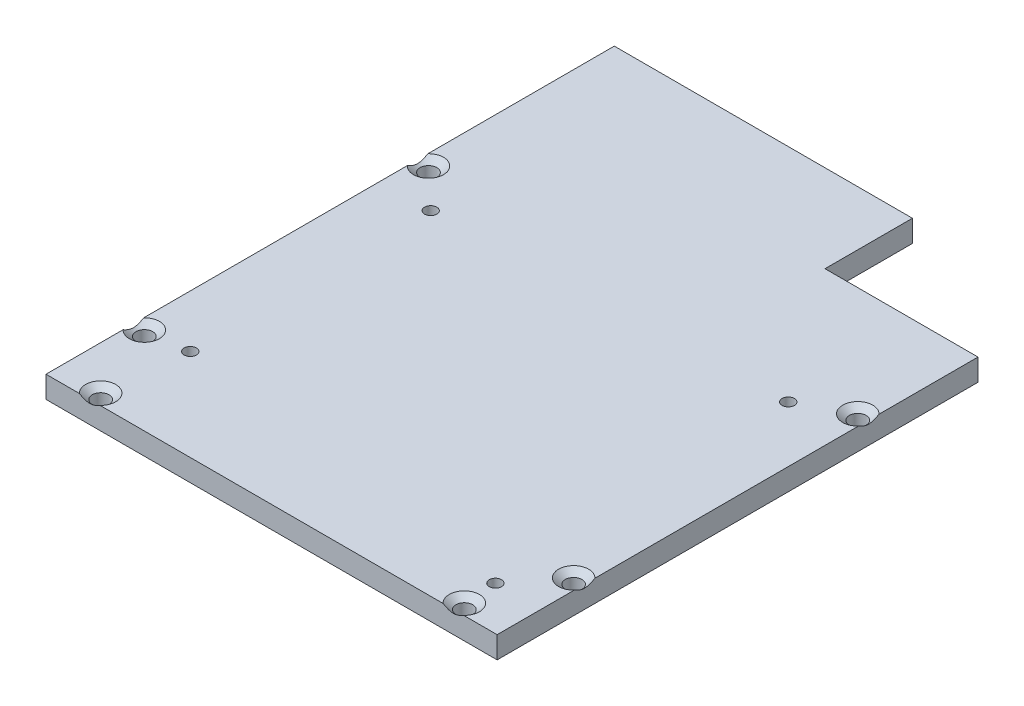
SolidWorks part; units mm, degrees
material "Delrin"
ref_plane "Front Plane" through (0, 0, 0) normal (0, 0, 1) x (1, 0, 0)
ref_plane "Top Plane" through (0, 0, 0) normal (0, 1, 0) x (1, 0, 0)
ref_plane "Right Plane" through (0, 0, 0) normal (1, 0, 0) x (0, 0, -1)
sketch "Sketch1" plane through (0, 0, 0) normal (0, 1, 0) x (1, 0, 0)
  line L1 (-32.766, 49.2125) -> (32.766, 49.2125)
  line L2 (-32.766, 49.2125) -> (-32.766, -33.3375)
  line L3 (-32.766, -33.3375) -> (32.766, -33.3375)
  line L4 (32.766, 49.2125) -> (32.766, -33.3375)
  dimension "D1" = 65.532
  dimension "D2" = 32.766
  dimension "D3" = 82.55
  dimension "D4" = 33.3375
extrude "Extrude1" add sketch "Sketch1" along normal blind 3.175
hole_wizard "CSK for #2 Flat Head Machine Screw (100)1" positions "3DSketch1" profile "Sketch2" countersink size "#2" standard "Ansi Inch" end condition through all
sketch3d "3DSketch1"
  line L0 (-32.766, 3.175, -49.2125) -> (-32.766, 3.175, 33.3375) construction
  line L1 (32.766, 3.175, 33.3375) -> (32.766, 3.175, -49.2125) construction
  line L2 (-32.766, 3.175, 33.3375) -> (32.766, 3.175, 33.3375) construction
  point P1 (-26.416, 3.175, 31.75)
  point P3 (26.416, 3.175, 31.75)
  point P9 (-31.1785, 3.175, -20.6375)
  point P11 (-31.1785, 3.175, 20.6375)
  point P13 (31.1785, 3.175, -20.6375)
  point P15 (31.1785, 3.175, 20.6375)
  dimension "D1" = 6.35
  dimension "D2" = 6.35
  dimension "D3" = 1.5875
  dimension "D4" = 1.5875
  dimension "D5" = 1.5875
  dimension "D6" = 1.5875
  dimension "D7" = 1.5875
  dimension "D8" = 1.5875
  dimension "D9" = 53.975
  dimension "D10" = 53.975
  dimension "D14" = 12.7
  dimension "D15" = 12.7
sketch "Sketch2" plane through (-26.416, 3.175, 31.75) normal (1, 0, 0) x (0, 0, 1)
  line L0 (0, 0) -> (0, 3.175)
  line L1 (0, 3.175) -> (1.2192, 3.175)
  line L2 (1.2192, 3.175) -> (1.2192, 0.8099)
  line L3 (1.2192, 0.8099) -> (2.1844, 0)
  line L5 (2.1844, 0) -> (0, 0)
  line L6 (-1.2192, 0.8099) -> (-2.1844, 0) construction
  line L11 (0, -6.35) -> (0, 107.95) construction
  dimension "Thru Hole Dia." = 2.4384
  dimension "Thru Hole Depth" = 3.175
  dimension "Near C'Sink Dia." = 4.3688
  dimension "Near C'Sink Angle" = 100
sketch "Sketch3" plane through (0, 3.175, 0) normal (0, 1, 0) x (-1, 0, 0)
  line L1 (-32.766, -49.2125) -> (-10.541, -49.2125)
  line L2 (-32.766, -49.2125) -> (-32.766, -36.5125)
  line L3 (-32.766, -36.5125) -> (-10.541, -36.5125)
  line L4 (-10.541, -49.2125) -> (-10.541, -36.5125)
  dimension "D1" = 22.225
  dimension "D2" = 12.7
extrude "Cut-Extrude1" cut sketch "Sketch3" against normal through all
hole_wizard "Tap Drill for #2 Tap1" positions "3DSketch2" profile "Sketch4" hole size "#2-56" standard "Ansi Inch"
sketch3d "3DSketch2"
  line L0 (-32.766, 0, 33.3375) -> (32.766, 0, 33.3375) construction
  line L2 (-32.766, 0, -49.2125) -> (-32.766, 0, 33.3375) construction
  point P0 (24.638, 0, -17.0815)
  point P2 (-25.4, 0, -15.1765)
  point P4 (-25.146, 0, 20.0025)
  point P6 (26.162, 0, 26.9875)
  dimension "D1" = 50.419
  dimension "D2" = 6.35
  dimension "D3" = 7.62
  dimension "D4" = 7.366
  dimension "D5" = 13.335
  dimension "D6" = 48.514
  dimension "D7" = 57.404
  dimension "D8" = 58.928
sketch "Sketch4" plane through (24.638, 0, -17.0815) normal (1, 0, 0) x (0, 0, -1)
  line L0 (0, 0) -> (0, 6.8842)
  line L1 (0, 6.8842) -> (0.889, 6.35)
  line L2 (0.889, 6.35) -> (0.889, 0)
  line L5 (0.889, 0) -> (0, 0)
  line L10 (0, 6.8842) -> (-0.889, 6.35) construction
  line L11 (0, -6.35) -> (0, 107.95) construction
  dimension "Hole Dia." = 1.778
  dimension "Hole Depth" = 6.35
  dimension "Drill Angle" = 118
